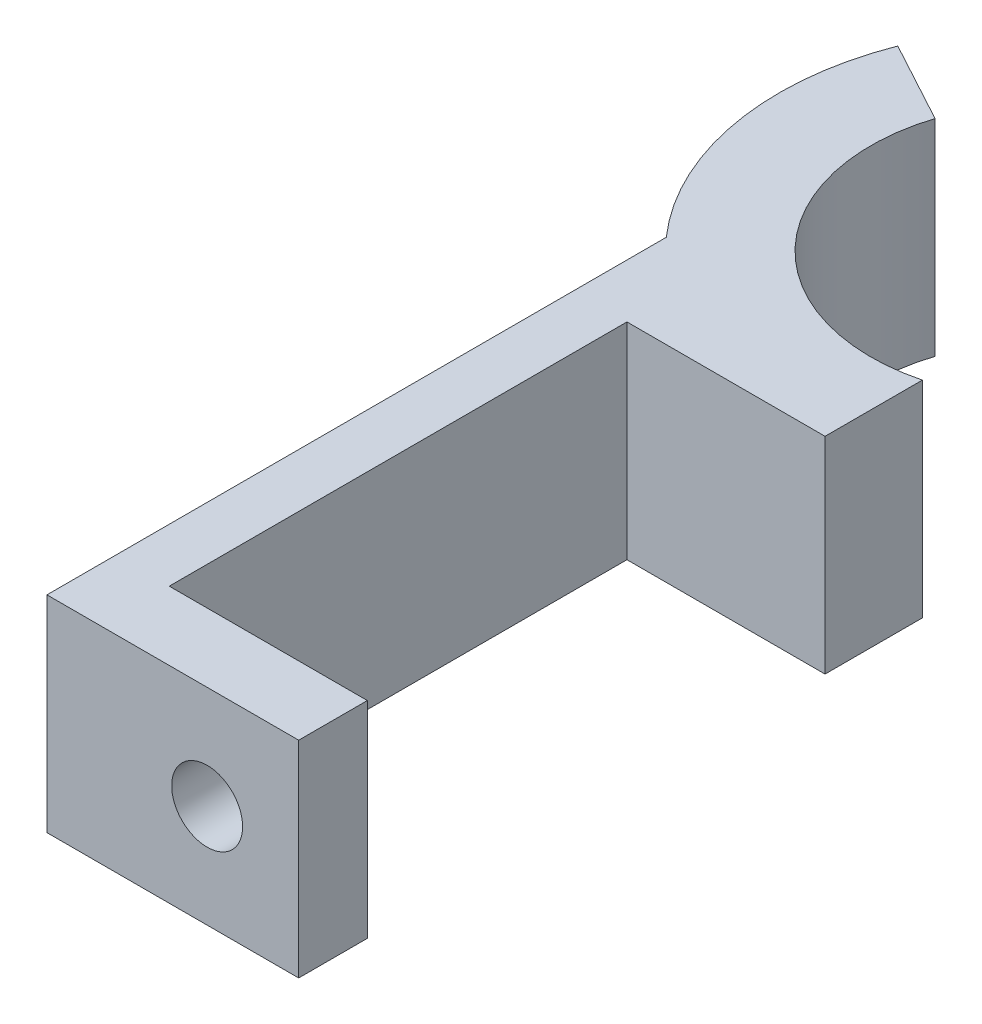
SolidWorks part; units mm, degrees
ref_plane "Front Plane" through (0, 0, 0) normal (0, 0, 1) x (1, 0, 0)
ref_plane "Top Plane" through (0, 0, 0) normal (0, 1, 0) x (1, 0, 0)
ref_plane "Right Plane" through (0, 0, 0) normal (1, 0, 0) x (0, 0, -1)
sketch "Sketch1" plane through (0, 0, 0) normal (0, 1, 0) x (1, 0, 0)
  line L0 (5.5, 14.254) -> (5.5, 10)
  line L1 (-5.5, -13) -> (5.5, -13)
  line L2 (-5.5, -13) -> (-5.5, 14.0627)
  line L5 (5.5, 10) -> (-3.1559, 10)
  line L6 (-3.1559, 10) -> (-3.1559, -10)
  line L8 (-7.6804, 26.3587) -> (-4.1224, 24.4288)
  line L9 (-3.1559, -10) -> (5.5, -10)
  line L10 (5.5, -10) -> (5.5, -13)
  arc A0 (-4.1224, 24.4288) -> (5.5, 14.254) centre (3.5, 22) ccw
  arc A1 (-7.6804, 26.3587) -> (-5.5, 14.0627) centre (3.5, 22) ccw
  point P0 (0, 0)
  dimension "D6" = 24
  dimension "D1" = 11
  dimension "D2" = 10
  dimension "D3" = 20
  dimension "D4" = 3
  dimension "D7" = 5.5
extrude "Boss-Extrude1" add sketch "Sketch1" along normal blind 9
sketch "Sketch2" plane through (0, 0, 13) normal (0, 0, 1) x (1, 0, 0)
  line L4 (-5.5, 0) -> (5.5, 0)
  line L5 (5.5, 0) -> (5.5, 9)
  line L6 (5.5, 9) -> (-5.5, 9)
  line L7 (-5.5, 9) -> (-5.5, 0)
  line L8 (-5.5, 0) -> (5.5, 0)
  line L10 (5.5, 9) -> (-5.5, 9)
  line L11 (-5.5, 9) -> (-5.5, 0)
  line L12 (5.5, 0) -> (5.5, 9)
  circle A0 centre (1.5, 4.5) radius 1.55
  dimension "D2" = 3.1
  dimension "D3" = 7
  dimension "D1" = 0
extrude "Cut-Extrude1" cut sketch "Sketch2" against normal blind 10 contours A0
